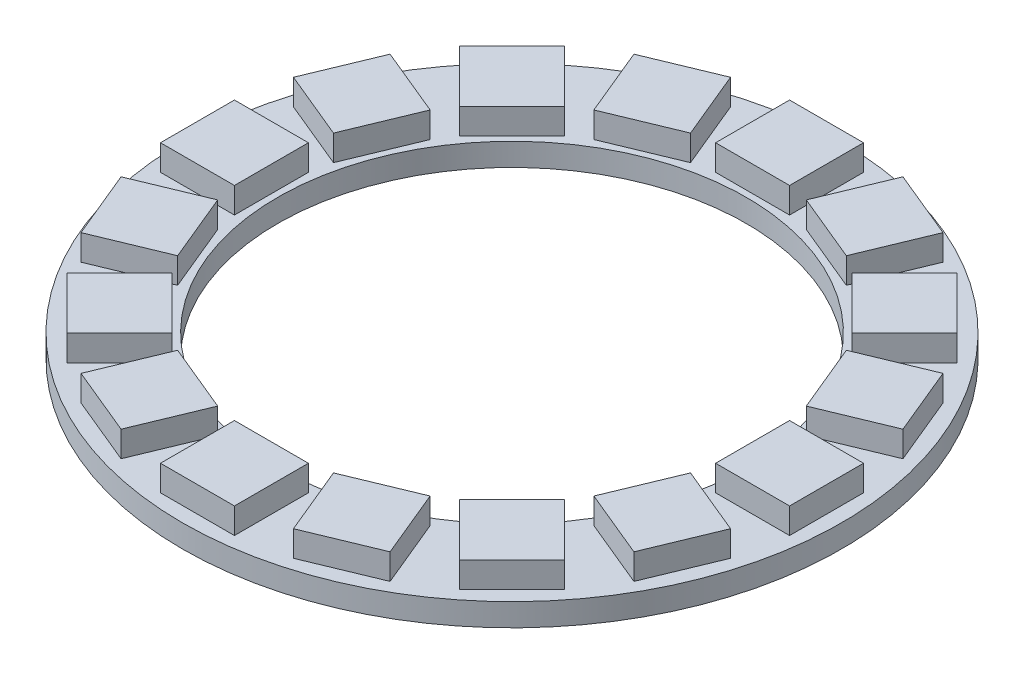
SolidWorks part; units mm, degrees
ref_plane "Front Plane" through (0, 0, 0) normal (0, 0, 1) x (1, 0, 0)
ref_plane "Top Plane" through (0, 0, 0) normal (0, 1, 0) x (1, 0, 0)
ref_plane "Right Plane" through (0, 0, 0) normal (1, 0, 0) x (0, 0, -1)
sketch "Sketch1" plane through (0, 0, 0) normal (0, 1, 0) x (1, 0, 0)
  circle A0 centre (0, 0) radius 22.5
  circle A1 centre (0, 0) radius 16
  dimension "D1" = 32
  dimension "D2" = 45
extrude "Boss-Extrude1" add sketch "Sketch1" along normal blind 1.55
sketch "Sketch2" plane through (0, 1.55, 0) normal (0, 1, 0) x (1, 0, 0)
  line L0 (0, 0) -> (0, 22.5) construction
  line L1 (-2.525, 16.425) -> (2.525, 16.425)
  line L2 (-2.525, 16.425) -> (-2.525, 21.475)
  line L3 (-2.525, 21.475) -> (2.525, 21.475)
  line L4 (2.525, 21.475) -> (2.525, 16.425)
  circle A0 centre (0, 0) radius 16.425 construction
  circle A1 centre (0, 0) radius 22.5 construction
  point P10 (0, 16.425)
  dimension "D1" = 32.85
  dimension "D2" = 5.05
  dimension "D3" = 5.05
extrude "Boss-Extrude2" add sketch "Sketch2" along normal blind 1.75
pattern_circular "CirPattern1" count 16 over 360 about axis through (0, 0, 0) along (0, 1, 0) of "Boss-Extrude2"
sketch "Sketch3" plane through (0, 0, 0) normal (0, -1, 0) x (1, 0, 0)
  line L0 (0, 0) -> (12.3319, -17.6118) construction
  line L1 (0, 0) -> (-17.6118, -12.3319) construction
  line L2 (0, 0) -> (-21.5, 0) construction
  line L3 (0, 0) -> (12.3319, 17.6118) construction
  line L4 (0, 0) -> (0, -7.5727) construction
  circle A0 centre (0, 0) radius 21.5 construction
  circle A1 centre (0, -21.5) radius 0.375
  circle A2 centre (0, 21.5) radius 0.375
  circle A3 centre (12.3319, -17.6118) radius 0.375
  circle A4 centre (-17.6118, -12.3319) radius 0.375
  circle A5 centre (-21.5, 0) radius 0.375
  circle A6 centre (12.3319, 17.6118) radius 0.375
  point P3 (0, -21.5)
  dimension "D1" = 43
  dimension "D2" = 0.75
  dimension "D3" = 35
  dimension "D4" = 35
  dimension "D5" = 35
extrude "Cut-Extrude1" [suppressed] cut sketch "Sketch3" against normal through all
equation "\"D3@Sketch2\"=\"D2@Sketch2\""
equation "\"D5@Sketch3\"=\"D4@Sketch3\""
